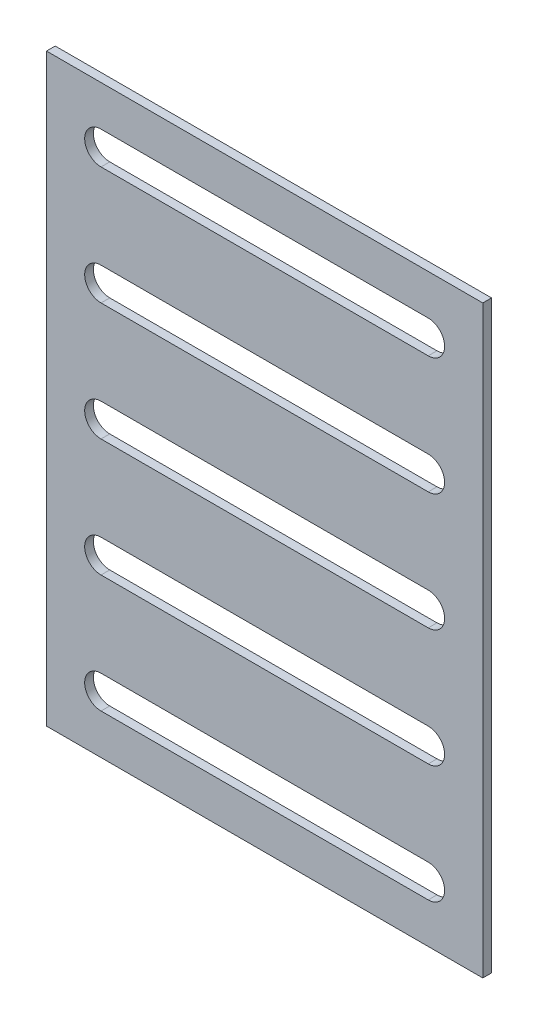
SolidWorks part; units mm, degrees
ref_plane "前视基准面" through (0, 0, 0) normal (0, 0, 1) x (1, 0, 0)
ref_plane "上视基准面" through (0, 0, 0) normal (0, 1, 0) x (1, 0, 0)
ref_plane "右视基准面" through (0, 0, 0) normal (1, 0, 0) x (0, 0, -1)
sketch "草图1" plane through (0, 0, 0) normal (0, 0, 1) x (1, 0, 0)
  line L1 (-100, 134) -> (100, 134)
  line L2 (-100, 134) -> (-100, -134)
  line L3 (-100, -134) -> (100, -134)
  line L4 (100, 134) -> (100, -134)
  dimension "D1" = 200
  dimension "D2" = 268
extrude "凸台-拉伸1" add sketch "草图1" along normal blind 4
sketch "草图2" plane through (0, 0, 4) normal (0, 0, 1) x (1, 0, 0)
  line L0 (100, 134) -> (-100, 134) construction
  line L3 (100, -134) -> (100, 134) construction
  line L5 (-100, -134) -> (100, -134) construction
  line L6 (-100, 134) -> (-100, -134) construction
  line L7 (-75, 115.5) -> (75, 115.5)
  line L9 (-75, 100.5) -> (75, 100.5)
  line L10 (-75, 61.5) -> (75, 61.5)
  line L11 (75, 46.5) -> (-75, 46.5)
  line L12 (-75, 7.5) -> (75, 7.5)
  line L13 (-75, -7.5) -> (75, -7.5)
  line L14 (-75, -46.5) -> (75, -46.5)
  line L15 (-75, -61.5) -> (75, -61.5)
  line L16 (-75, -100.5) -> (75, -100.5)
  line L17 (-75, -115.5) -> (75, -115.5)
  arc A2 (-75, 115.5) -> (-75, 100.5) centre (-75, 108) ccw
  arc A3 (-75, -100.5) -> (-75, -115.5) centre (-75, -108) ccw
  arc A4 (75, -115.5) -> (75, -100.5) centre (75, -108) ccw
  arc A5 (75, 100.5) -> (75, 115.5) centre (75, 108) ccw
  arc A6 (-75, 7.5) -> (-75, -7.5) centre (-75, 0) ccw
  arc A7 (75, -7.5) -> (75, 7.5) centre (75, 0) ccw
  arc A8 (-75, 61.5) -> (-75, 46.5) centre (-75, 54) ccw
  arc A9 (75, 46.5) -> (75, 61.5) centre (75, 54) ccw
  arc A10 (-75, -46.5) -> (-75, -61.5) centre (-75, -54) ccw
  arc A11 (75, -61.5) -> (75, -46.5) centre (75, -54) ccw
  dimension "D1" = 26
  dimension "D2" = 26
  dimension "D3" = 25
  dimension "D4" = 25
  dimension "D5" = 25
  dimension "D6" = 26
  dimension "D7" = 26
extrude "切除-拉伸1" cut sketch "草图2" against normal through all
